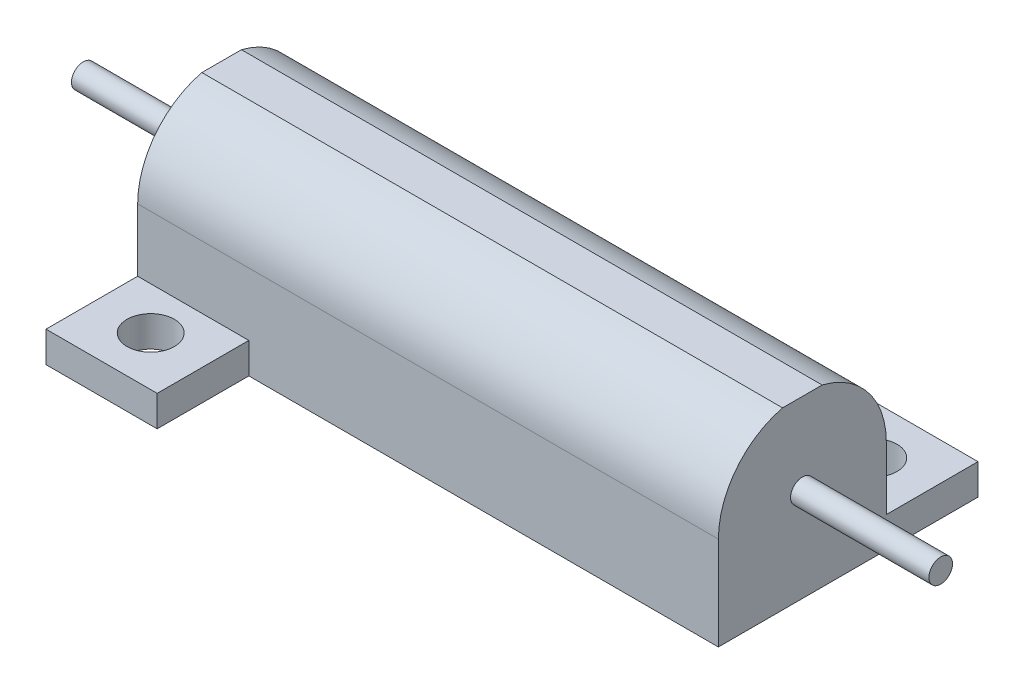
SolidWorks part; units mm, degrees
ref_plane "Płaszczyzna przednia" through (0, 0, 0) normal (0, 0, 1) x (1, 0, 0)
ref_plane "Płaszczyzna górna" through (0, 0, 0) normal (0, 1, 0) x (1, 0, 0)
ref_plane "Płaszczyzna prawa" through (0, 0, 0) normal (1, 0, 0) x (0, 0, -1)
sketch "Szkic1" plane through (0, 0, 0) normal (0, 1, 0) x (1, 0, 0)
  line L0 (0, 0) -> (0, 21.95)
  line L1 (0, 21.95) -> (39.7, 21.95)
  line L2 (39.7, 21.95) -> (39.7, 29.7)
  line L3 (39.7, 29.7) -> (49.1, 29.7)
  line L4 (49.1, 29.7) -> (49.1, 7.75)
  line L5 (49.1, 7.75) -> (9.4, 7.75)
  line L6 (9.4, 7.75) -> (9.4, 0)
  line L7 (9.4, 0) -> (0, 0)
  circle A0 centre (4.7, 4.15) radius 2
  circle A2 centre (44.4, 25.55) radius 2
  dimension "D11" = 4
  dimension "D12" = 4
  dimension "D1" = 49.1
  dimension "D2" = 29.7
  dimension "D3" = 14.2
  dimension "D4" = 21.95
  dimension "D5" = 9.4
  dimension "D6" = 9.4
  dimension "D7" = 39.7
  dimension "D8" = 21.4
  dimension "D9" = 4.7
  dimension "D10" = 4.15
extrude "Dodanie-wyciągnięcie1" add sketch "Szkic1" along normal blind 2.6 contours L1 L2 L3 L4 L5 L6 L7 L0
sketch "Szkic4" plane through (0, 0, 0) normal (0, -1, 0) x (1, 0, 0)
  line L3 (0, 0) -> (0, -21.95) construction
  line L5 (9.4, 0) -> (0, 0) construction
  circle A0 centre (4.7, -4.15) radius 2
  circle A1 centre (44.4, -25.55) radius 2
  dimension "D1" = 4
  dimension "D2" = 4
  dimension "D3" = 39.7
  dimension "D4" = 21.4
  dimension "D5" = 4.7
  dimension "D6" = 4.15
extrude "Wytnij-wyciągnięcie1" cut sketch "Szkic4" against normal blind 2.6 contours A1 | A0
sketch "Szkic5" plane through (0, 2.6, 0) normal (0, 1, 0) x (1, 0, 0)
  line L0 (49.1, 29.7) -> (49.1, 7.75) construction
  line L1 (0, 7.75) -> (49.1, 7.75)
  line L2 (0, 7.75) -> (0, 21.95)
  line L3 (0, 21.95) -> (49.1, 21.95)
  line L4 (49.1, 7.75) -> (49.1, 21.95)
  dimension "D1" = 14.2
  dimension "D2" = 49.1
extrude "Dodanie-wyciągnięcie3" add sketch "Szkic5" along normal blind 5.3
sketch "Szkic7" plane through (0, 0, 0) normal (1, 0, 0) x (0, 0, -1)
  line L0 (13.1767, 14.8) -> (16.5233, 14.8)
  line L1 (16.335, 0) -> (-16.335, 0) construction
  arc A0 (13.1767, 14.8) -> (16.5233, 14.8) centre (14.85, 7.9) ccw
  dimension "D1" = 14.2
  dimension "D2" = 14.8
extrude "Dodanie-wyciągnięcie4" add sketch "Szkic7" along normal blind 49.1 contours A0 L0
sketch "Szkic10" plane through (0, 0, 0) normal (-1, 0, 0) x (0, 0, 1)
  line L0 (-7.75, 7.9) -> (-7.75, 0) construction
  line L2 (-29.7, 2.6) -> (-21.95, 2.6) construction
  circle A0 centre (-14.85, 7.9) radius 1
  dimension "D1" = 2
  dimension "D2" = 7.1
  dimension "D3" = 5.3
extrude "Dodanie-wyciągnięcie5" add sketch "Szkic10" along normal blind 11.7 and the other way blind 60.8
